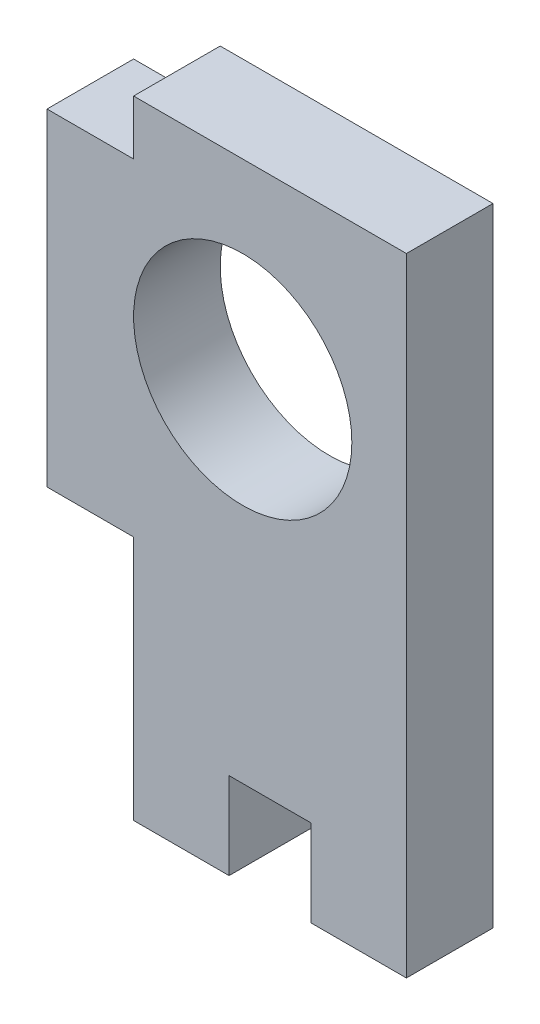
SolidWorks part; units mm, degrees
ref_plane "Front Plane" through (0, 0, 0) normal (0, 0, 1) x (1, 0, 0)
ref_plane "Top Plane" through (0, 0, 0) normal (0, 1, 0) x (1, 0, 0)
ref_plane "Right Plane" through (0, 0, 0) normal (1, 0, 0) x (0, 0, -1)
sketch "Sketch2" plane through (0, 0, 0) normal (0, 0, 1) x (1, 0, 0)
  line L0 (-1, 0.5) -> (5, 0.5) construction
  line L1 (-5, -11.5) -> (-1.5, -11.5)
  line L2 (-5, -11.5) -> (-5, -2.5)
  line L3 (-5, 11.5) -> (-1.5, 11.5)
  line L4 (5, -11.5) -> (5, 11.5)
  line L5 (-5, 4.5) -> (1.9565, 4.5) construction
  line L6 (1.5, 11.5) -> (5, 11.5)
  line L7 (-1.5, 11.5) -> (1.5, 11.5)
  line L8 (-1, 11.5) -> (-1, 0.5) construction
  line L9 (-5, 9.5) -> (-8.175, 9.5)
  line L10 (-8.175, 9.5) -> (-8.175, -2.5)
  line L11 (-8.175, -2.5) -> (-5, -2.5)
  line L13 (0, 0) -> (5, -11.5) construction
  line L14 (0.2174, 0.5) -> (0, 0) construction
  line L15 (0, 0) -> (-5, -11.5) construction
  line L16 (-0.2174, 0.5) -> (0, 0) construction
  line L17 (5, 0) -> (0, 0) construction
  line L18 (1.5, -8.325) -> (1.5, -11.5)
  line L19 (-1.5, -8.325) -> (1.5, -8.325)
  line L20 (-1.5, -8.325) -> (-1.5, -11.5)
  line L21 (1.5, -11.5) -> (5, -11.5)
  line L22 (0, 0.5) -> (0, -8.325) construction
  line L23 (-5, 9.5) -> (-5, 11.5)
  circle A0 centre (-1, 4.5) radius 4
  point P0 (0, 0)
  point P10 (0, 10.9251)
  dimension "D1" = 10
  dimension "D2" = 23
  dimension "D3" = 12
  dimension "D4" = 4
  dimension "D5" = 4
  dimension "D6" = 3.175
  dimension "D7" = 12
  dimension "D8" = 9
  dimension "D9" = 3.5
extrude "Boss-Extrude1" add sketch "Sketch2" against normal blind 3.175 contours A0 | L9 L10 L11 L2 L1 L20 L19 L18 L21 L4 L6 L7 L3 L23
